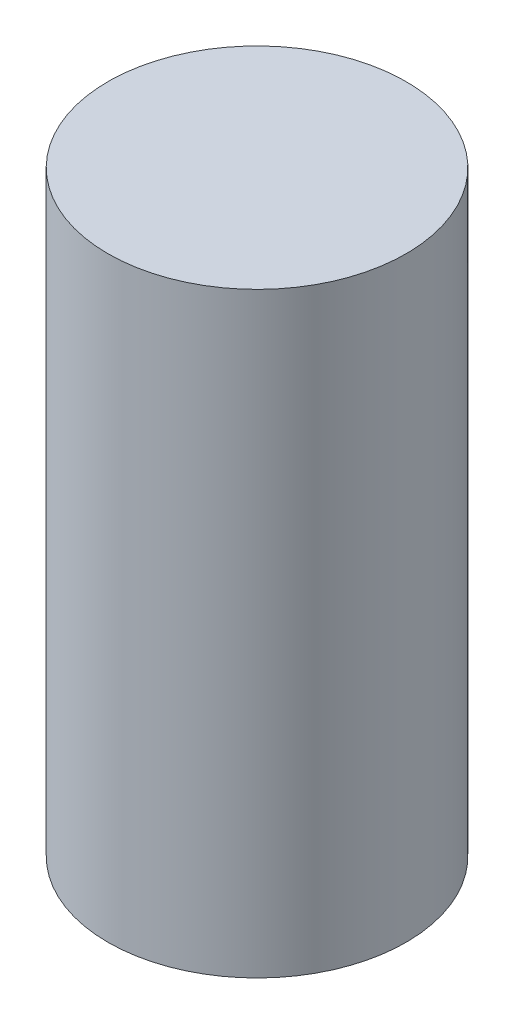
SolidWorks part; units mm, degrees
ref_plane "Front Plane" through (0, 0, 0) normal (0, 0, 1) x (1, 0, 0)
ref_plane "Top Plane" through (0, 0, 0) normal (0, 1, 0) x (1, 0, 0)
ref_plane "Right Plane" through (0, 0, 0) normal (1, 0, 0) x (0, 0, -1)
sketch "Sketch2" plane through (0, 0, 0) normal (0, 1, 0) x (1, 0, 0)
  circle A0 centre (0, 0) radius 15
  dimension "D1" = 30
extrude "Boss-Extrude1" add sketch "Sketch2" along normal blind 60
